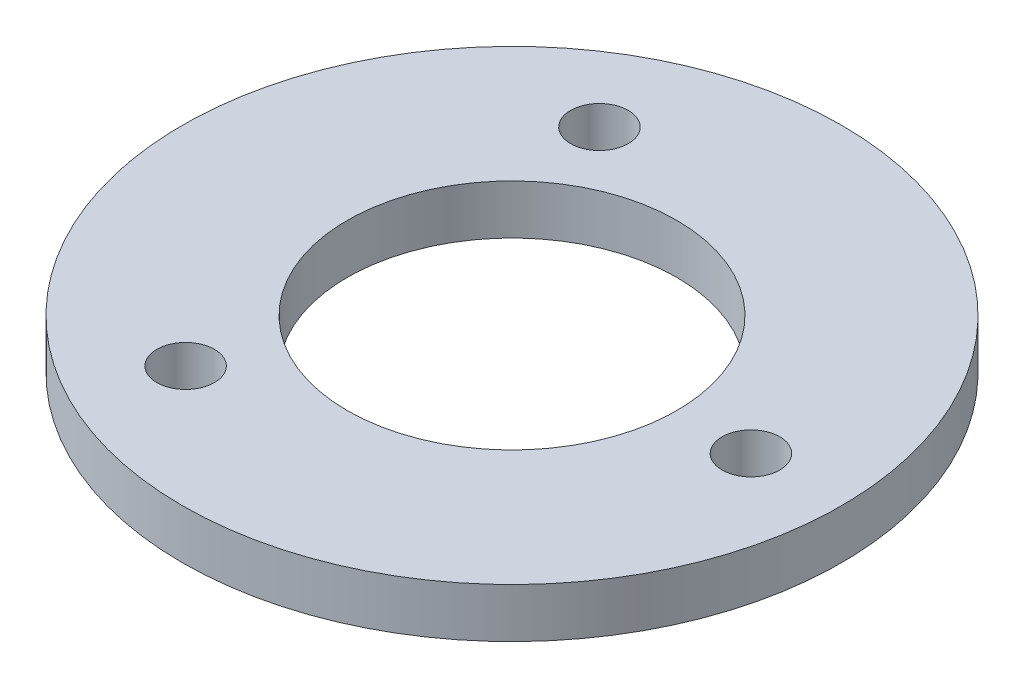
SolidWorks part; units mm, degrees
ref_plane "Front Plane" through (0, 0, 0) normal (0, 0, 1) x (1, 0, 0)
ref_plane "Top Plane" through (0, 0, 0) normal (0, 1, 0) x (1, 0, 0)
ref_plane "Right Plane" through (0, 0, 0) normal (1, 0, 0) x (0, 0, -1)
sketch "Sketch1" plane through (0, 0, 0) normal (0, 1, 0) x (1, 0, 0)
  line L0 (0, 0) -> (14.5, 0) construction
  line L1 (-7.25, 12.5574) -> (0, 0) construction
  circle A0 centre (0, 0) radius 20
  circle A1 centre (0, 0) radius 10
  circle A2 centre (14.5, 0) radius 1.75
  circle A3 centre (-7.25, -12.5574) radius 1.75
  circle A4 centre (-7.25, 12.5574) radius 1.75
  dimension "D1" = 40
  dimension "D2" = 20
  dimension "D3" = 3.5
  dimension "D4" = 14.5
  dimension "D6" = 7.25
  dimension "D5" = 3
extrude "Boss-Extrude1" add sketch "Sketch1" along normal blind 3
